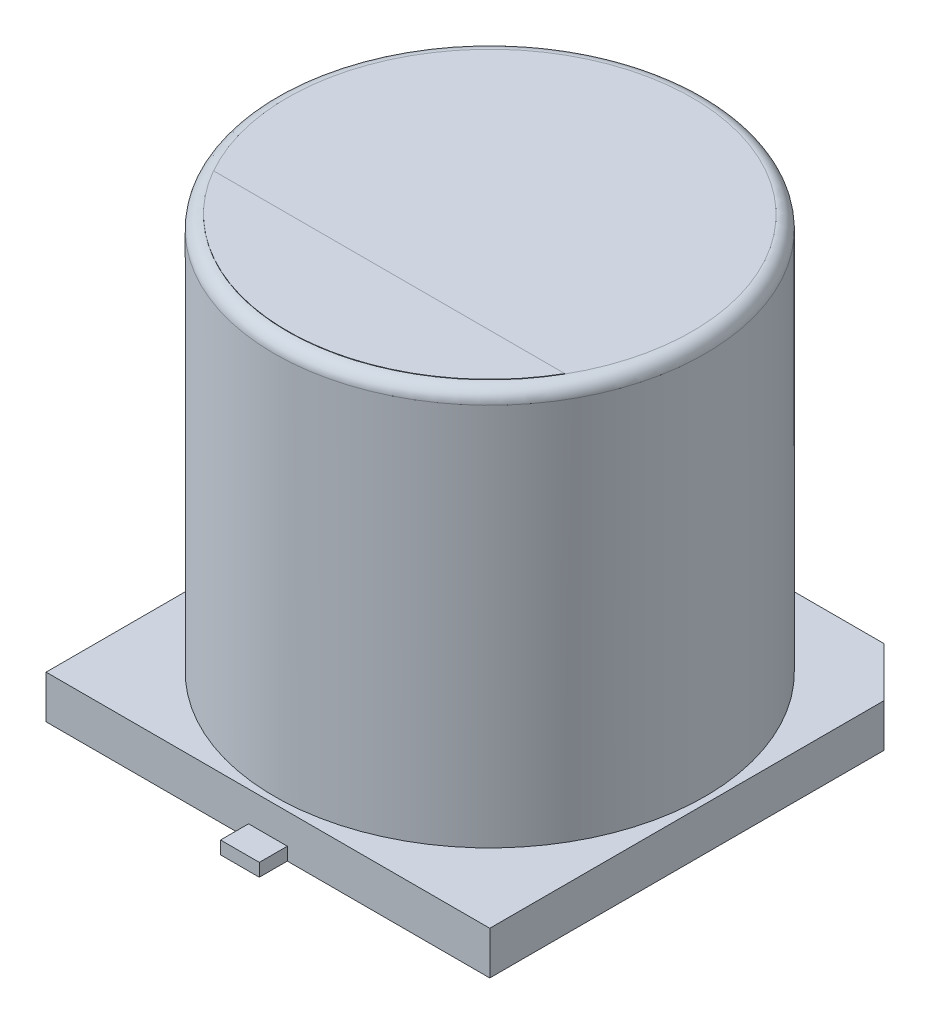
SolidWorks part; units mm, degrees
ref_plane "Front Plane" through (0, 0, 0) normal (0, 0, 1) x (1, 0, 0)
ref_plane "Top Plane" through (0, 0, 0) normal (0, 1, 0) x (1, 0, 0)
ref_plane "Right Plane" through (0, 0, 0) normal (1, 0, 0) x (0, 0, -1)
sketch "Sketch2" plane through (0, 0, 0) normal (0, 1, 0) x (1, 0, 0)
  line L0 (0, 0) -> (0, 2.085) construction
  line L1 (0, 0) -> (2.9643, 0) construction
  line L2 (5.15, -5.15) -> (-5.15, -5.15)
  line L3 (-5.15, -5.15) -> (-5.15, 4)
  line L4 (-5.15, 4) -> (-4, 5.15)
  line L5 (-4, 5.15) -> (4, 5.15)
  line L6 (4, 5.15) -> (5.15, 4)
  line L7 (5.15, 4) -> (5.15, -5.15)
  line L8 (0, -5.15) -> (0, -0.9795) construction
  line L9 (0, 5.15) -> (0, 2.1922) construction
  line L10 (-0.2934, -5.15) -> (-0.2934, 5.15) construction
  line L11 (-0.2934, 0) -> (-0.8682, 0) construction
  dimension "D1" = 10.3
  dimension "D2" = 10.3
  dimension "D3" = 8
extrude "Boss-Extrude1" add sketch "Sketch2" along normal blind 1
sketch "Sketch3" plane through (0, 0, 0) normal (0, 1, 0) x (1, 0, 0)
  circle A0 centre (0, 0) radius 5
  dimension "D1" = 10
extrude "Boss-Extrude2" add sketch "Sketch3" along normal blind 10.2 contours A0
fillet "Fillet1" radius 0.3 1 edges at (0, 10.2, 5)
sketch "Sketch4" plane through (0, 0, 0) normal (0, 1, 0) x (1, 0, 0)
  line L0 (0, 0) -> (0.232, 0) construction
  line L1 (0.45, 5.8) -> (-0.45, 5.8)
  line L2 (0.45, -2.3) -> (-0.45, -2.3)
  line L3 (0.45, -2.3) -> (0.45, -5.8)
  line L4 (0.45, -5.8) -> (-0.45, -5.8)
  line L5 (-0.45, -2.3) -> (-0.45, -5.8)
  line L6 (0.45, -2.3) -> (-0.45, -5.8) construction
  line L7 (0.45, -5.8) -> (-0.45, -2.3) construction
  line L8 (-0.45, 2.3) -> (-0.45, 5.8)
  line L9 (0.45, 2.3) -> (-0.45, 2.3)
  line L10 (0.45, 2.3) -> (0.45, 5.8)
  line L11 (0.45, 5.8) -> (-0.45, 2.3) construction
  line L12 (0.45, 2.3) -> (-0.45, 5.8) construction
  point P1 (0, -4.05)
  point P12 (0, 4.05)
  dimension "D1" = 0.9
  dimension "D2" = 3.5
  dimension "D3" = 4.6
extrude "Boss-Extrude3" add sketch "Sketch4" along normal blind 0.3
ref_plane "Plane1" through (0, 10.2, 0) normal (0, 1, 0) x (1, 0, 0)
sketch "Sketch5" plane through (0, 10.2, 0) normal (0, 1, 0) x (1, 0, 0)
  line L0 (-4.0779, -2.3369) -> (4.0779, -2.3369)
  arc A1 (-4.0779, -2.3369) -> (4.0779, -2.3369) centre (0, 0) ccw
extrude "Boss-Extrude4" add sketch "Sketch5" along normal blind 0.01
